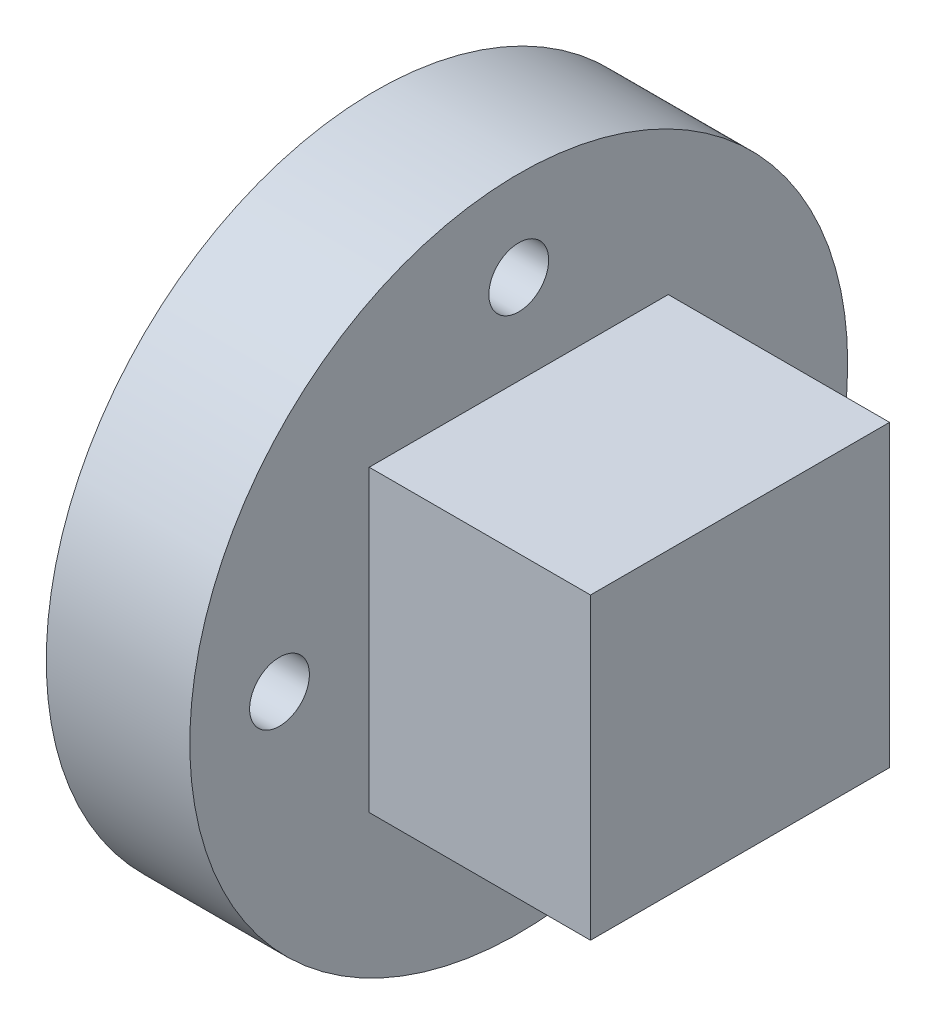
SolidWorks part; units mm, degrees
ref_plane "Front Plane" through (0, 0, 0) normal (0, 0, 1) x (1, 0, 0)
ref_plane "Top Plane" through (0, 0, 0) normal (0, 1, 0) x (1, 0, 0)
ref_plane "Right Plane" through (0, 0, 0) normal (1, 0, 0) x (0, 0, -1)
sketch "Sketch1" plane through (0, 0, 0) normal (1, 0, 0) x (0, 0, -1)
  line L0 (-1.3212, 1.6) -> (1.3212, 1.6)
  arc A0 (-1.3212, 1.6) -> (1.3212, 1.6) centre (0, 0) ccw
  circle A1 centre (0, 0) radius 5.5
  circle A2 centre (0, 4) radius 0.5
  circle A3 centre (4, 0) radius 0.5
  circle A4 centre (0, -4) radius 0.5
  circle A5 centre (-4, 0) radius 0.5
  point P16 (0, 0)
  dimension "D1" = 4.15
  dimension "D3" = 11
  dimension "D5" = 1
  dimension "D2" = 1.6
  dimension "D4" = 4
  dimension "D6" = 4
extrude "Boss-Extrude1" add sketch "Sketch1" along normal blind 6
sketch "Sketch2" plane through (6, 0, 0) normal (1, 0, 0) x (0, 0, -1)
  circle A0 centre (0, 0) radius 5.5
extrude "Boss-Extrude2" add sketch "Sketch2" against normal blind 1
sketch "Sketch3" plane through (0, 0, 0) normal (-1, 0, 0) x (0, 0, 1)
  circle A0 centre (0, 4) radius 0.5
  circle A1 centre (4, 0) radius 0.5
  circle A2 centre (0, -4) radius 0.5
  circle A3 centre (-4, 0) radius 0.5
  point P12 (0, 0)
  dimension "D1" = 4
extrude "Cut-Extrude1" cut sketch "Sketch3" against normal through all
sketch "Sketch4" plane through (6, 0, 0) normal (1, 0, 0) x (0, 0, -1)
  line L1 (-2.5, 2.5) -> (2.5, 2.5)
  line L2 (-2.5, 2.5) -> (-2.5, -2.5)
  line L3 (-2.5, -2.5) -> (2.5, -2.5)
  line L4 (2.5, 2.5) -> (2.5, -2.5)
  dimension "D1" = 5
  dimension "D2" = 5
  dimension "D3" = 2.5
  dimension "D4" = 2.5
extrude "Boss-Extrude3" add sketch "Sketch4" along normal blind 0.1
sketch "Sketch5" plane through (6, 0, 0) normal (1, 0, 0) x (0, 0, -1)
  line L1 (-2.5, 2.5) -> (2.5, 2.5)
  line L2 (-2.5, 2.5) -> (-2.5, -2.5)
  line L3 (-2.5, -2.5) -> (2.5, -2.5)
  line L4 (2.5, 2.5) -> (2.5, -2.5)
extrude "Cut-Extrude2" cut sketch "Sketch5" against normal blind 3.6 flip side to cut
